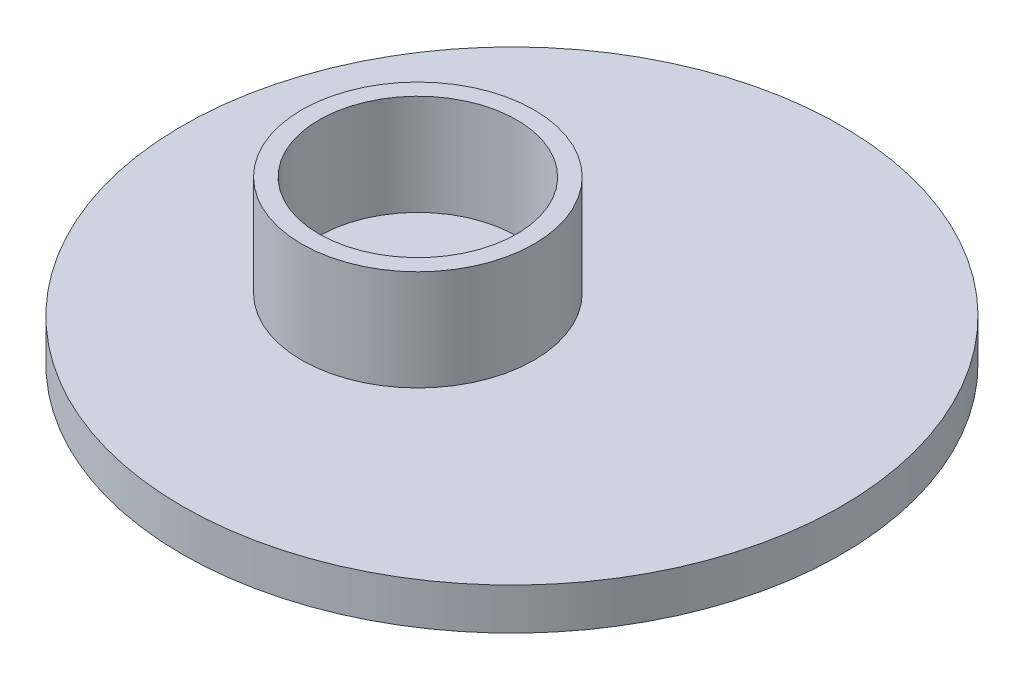
SolidWorks part; units mm, degrees
ref_plane "Front Plane" through (0, 0, 0) normal (0, 0, 1) x (1, 0, 0)
ref_plane "Top Plane" through (0, 0, 0) normal (0, 1, 0) x (1, 0, 0)
ref_plane "Right Plane" through (0, 0, 0) normal (1, 0, 0) x (0, 0, -1)
sketch "Sketch1" plane through (0, 0, 0) normal (0, 1, 0) x (1, 0, 0)
  circle A0 centre (0, 0) radius 9.5
extrude "Boss-Extrude1" add sketch "Sketch1" along normal blind 1.2
sketch "Sketch2" plane through (0, 1.2, 0) normal (0, 1, 0) x (1, 0, 0)
  line L0 (-1.9278, 3.7162) -> (-1.9278, -5.2838) construction
  circle A0 centre (-1.9278, -0.7838) radius 4.5 construction
  circle A1 centre (-1.9278, -0.7838) radius 3.35
  circle A2 centre (-1.9278, -0.7838) radius 2.85
extrude "Boss-Extrude2" add sketch "Sketch2" along normal blind 2.9
